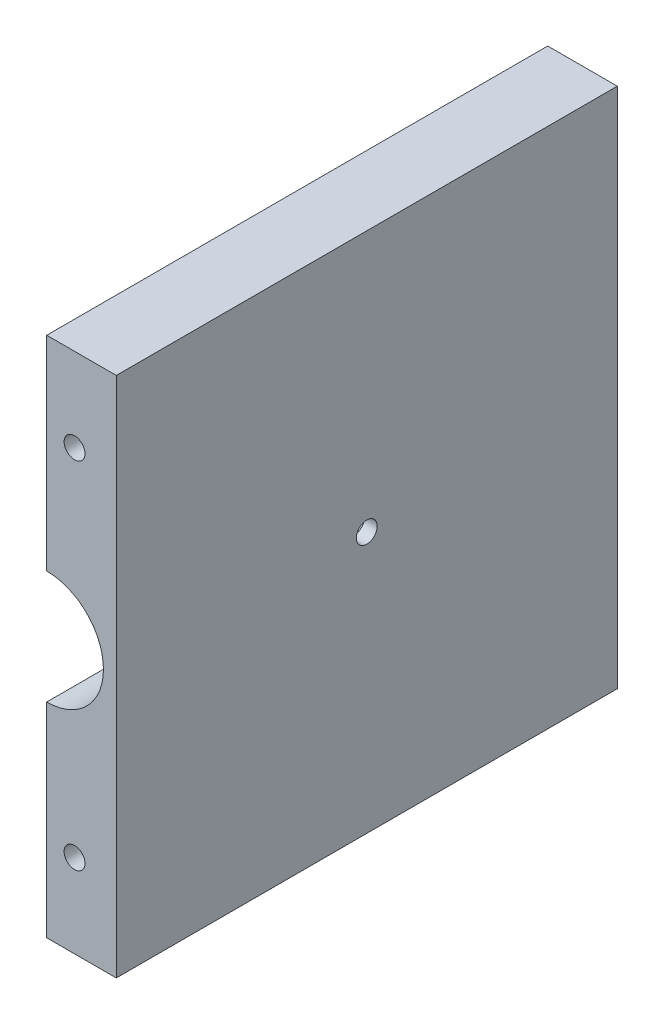
SolidWorks part; units mm, degrees
ref_plane "Front Plane" through (0, 0, 0) normal (0, 0, 1) x (1, 0, 0)
ref_plane "Top Plane" through (0, 0, 0) normal (0, 1, 0) x (1, 0, 0)
ref_plane "Right Plane" through (0, 0, 0) normal (1, 0, 0) x (0, 0, -1)
sketch "Croquis1" plane through (0, 0, 0) normal (0, 0, 1) x (1, 0, 0)
  line L1 (0, 0) -> (10, 0)
  line L3 (0, 75) -> (10, 75)
  line L4 (10, 0) -> (10, 75)
  line L5 (10, 37.5) -> (-24.9857, 37.5) construction
  line L14 (0, 75) -> (0, 45.65)
  line L15 (0, 0) -> (0, 29.35)
  arc A0 (0, 29.35) -> (0, 45.65) centre (0, 37.5) ccw
  point P13 (8.15, 37.5)
extrude "Saliente-Extruir1" add sketch "Croquis1" along normal blind 72 contours L4 L3 L14 A0 L15 L1
sketch "Croquis2" plane through (0, 0, 72) normal (0, 0, 1) x (1, 0, 0)
  line L2 (0, 75) -> (10, 75) construction
  line L3 (0, 0) -> (10, 0) construction
  line L4 (10, 0) -> (10, 75) construction
  circle A0 centre (4, 63) radius 1.5
  circle A1 centre (4, 12) radius 1.5
extrude "Cortar-Extruir1" cut sketch "Croquis2" against normal through all
sketch "Croquis3" plane through (10, 0, 0) normal (1, 0, 0) x (0, 0, -1)
  line L0 (-72, 37.5) -> (0, 37.5) construction
  line L1 (-72, 0) -> (-72, 75) construction
  line L2 (0, 0) -> (0, 75) construction
  circle A0 centre (-36, 37.5) radius 1.5
extrude "Cortar-Extruir2" cut sketch "Croquis3" against normal through all
equation "\"alto\"= 75mm"
equation "\"ancho\"= 10mm"
equation "\"diametro\"= 16.3mm"
equation "\"D2@Croquis1\"=\"alto\""
equation "\"D1@Croquis1\"=\"ancho\""
equation "\"D3@Croquis1\"=\"diametro\""
equation "\"r3\"= 3mm"
equation "\"sep\"= 12mm'sepa"
equation "\"sepancho\"= 6mm"
equation "\"D5@Croquis2\"=\"r3\""
equation "\"D6@Croquis2\"=\"r3\""
equation "\"D3@Croquis2\"=\"sep\""
equation "\"D4@Croquis2\"=\"sep\""
equation "\"D1@Croquis2\"=\"sepancho\""
equation "\"D2@Croquis2\"=\"sepancho\""
equation "\"D1@Croquis3\"=\"r3\""
